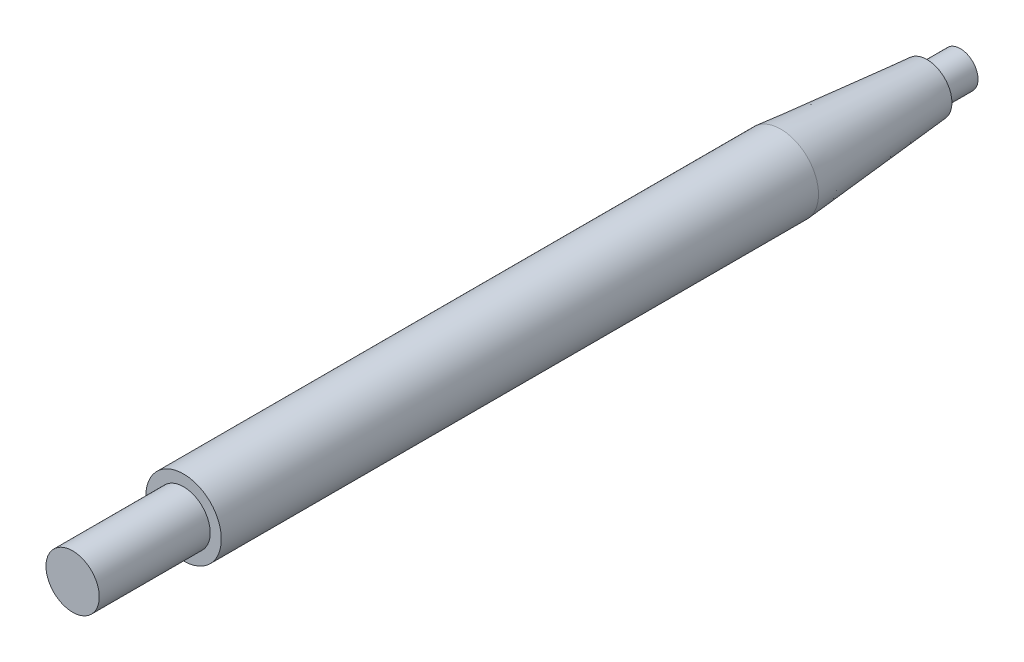
SolidWorks part; units mm, degrees
material "Plain Carbon Steel"
ref_plane "Front Plane" through (0, 0, 0) normal (0, 0, 1) x (1, 0, 0)
ref_plane "Top Plane" through (0, 0, 0) normal (0, 1, 0) x (1, 0, 0)
ref_plane "Right Plane" through (0, 0, 0) normal (1, 0, 0) x (0, 0, -1)
sketch "Base Sketch" plane through (0, 0, 0) normal (0, 1, 0) x (1, 0, 0)
  line L0 (-11.2254, 153.9926) -> (-12.8435, 153.9926)
  line L10 (-8.3435, -13.5074) -> (-8.3435, 121.0526)
  line L11 (-8.3435, 121.0526) -> (-11.2254, 153.9926)
  line L14 (-12.8435, 161.4926) -> (-16.8435, 161.4926)
  line L15 (-16.8435, 161.4926) -> (-16.8435, -13.5074)
  line L16 (-12.8435, 153.9926) -> (-12.8435, 161.4926)
  line L17 (-8.3435, -13.5074) -> (-10.8435, -13.5074)
  line L18 (-10.8435, -13.5074) -> (-10.8435, -38.5074)
  line L19 (-10.8435, -38.5074) -> (-16.8435, -38.5074)
  line L20 (-16.8435, -38.5074) -> (-16.8435, -13.5074)
  dimension "D1" = 8.5
  dimension "D2" = 185
  dimension "D3" = 32.94
  dimension "D4" = 7.5
  dimension "D6" = 4
  dimension "D5" = 6
  dimension "D7" = 25
  dimension "D8" = 200
revolve "Revolve1" add sketch "Base Sketch" angle 360 about L15
cosmetic thread "Pump Mounting Threads"
cosmetic thread "Motor Mounting Threads"
equation "\"Impeller_Length\"= 33.94mm"
equation "\"Shaft_Length\"= 200mm"
equation "\"D3@Base Sketch\"=\"Impeller_Length\" - 1"
equation "\"D8@Base Sketch\"=\"Shaft_Length\""
equation "\"Motor_Shaft_ID\"= 12mm"
equation "\"D5@Base Sketch\"=\"Motor_Shaft_ID\"/2"
equation "\"Motor_Shaft_Length\"= 25mm"
equation "\"D7@Base Sketch\"=\"Motor_Shaft_Length\""
